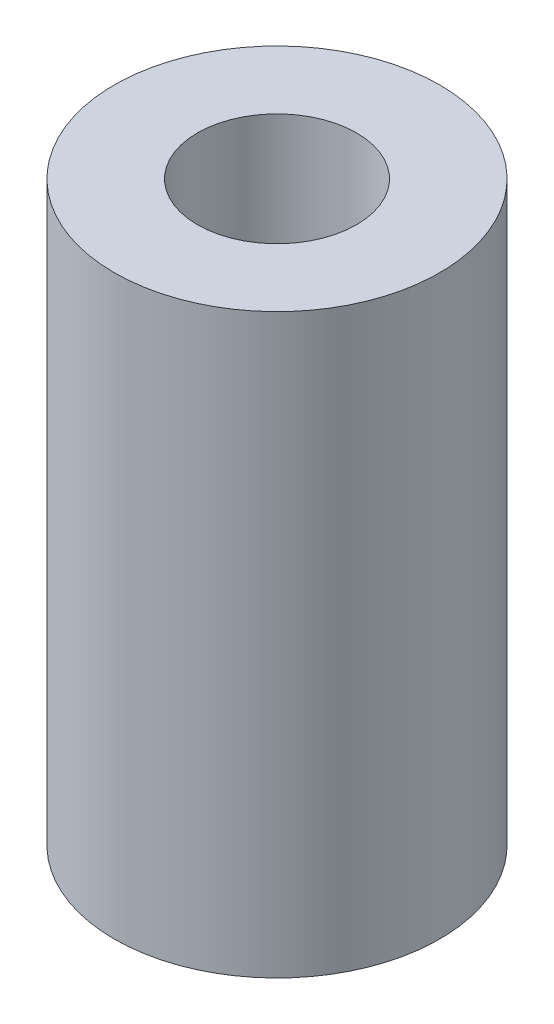
SolidWorks part; units mm, degrees
material "Propellant"
ref_plane "Front Plane" through (0, 0, 0) normal (0, 0, 1) x (1, 0, 0)
ref_plane "Top Plane" through (0, 0, 0) normal (0, 1, 0) x (1, 0, 0)
ref_plane "Right Plane" through (0, 0, 0) normal (1, 0, 0) x (0, 0, -1)
sketch "Sketch1" plane through (0, 0, 0) normal (0, 1, 0) x (1, 0, 0)
  circle A0 centre (0, 0) radius 32.4612
  circle A1 centre (0, 0) radius 15.875
extrude "Boss-Extrude1" add sketch "Sketch1" along normal blind 115.1467
